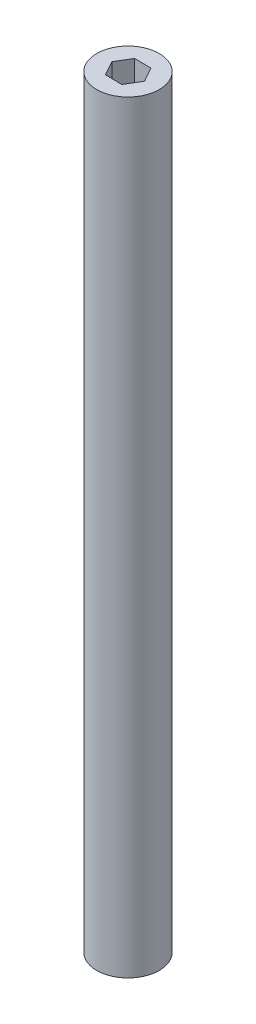
SolidWorks part; units mm, degrees
ref_plane "Front Plane" through (0, 0, 0) normal (0, 0, 1) x (1, 0, 0)
ref_plane "Top Plane" through (0, 0, 0) normal (0, 1, 0) x (1, 0, 0)
ref_plane "Right Plane" through (0, 0, 0) normal (1, 0, 0) x (0, 0, -1)
sketch "Sketch1" plane through (0, 0, 0) normal (0, 1, 0) x (1, 0, 0)
  line L0 (3.2966, -5.8306) -> (6.7657, -0.0446)
  line L1 (6.7657, -0.0446) -> (3.4894, 5.8527)
  line L2 (3.4894, 5.8527) -> (-3.2559, 5.964)
  line L3 (-3.2559, 5.964) -> (-6.725, 0.178)
  line L4 (-6.725, 0.178) -> (-3.4487, -5.7193)
  line L5 (-3.4487, -5.7193) -> (3.2966, -5.8306)
  circle A0 centre (0, 0) radius 12.698
  circle A1 centre (0.0203, 0.0667) radius 5.8424 construction
extrude "Boss-Extrude1" add sketch "Sketch1" along normal blind 309.88
